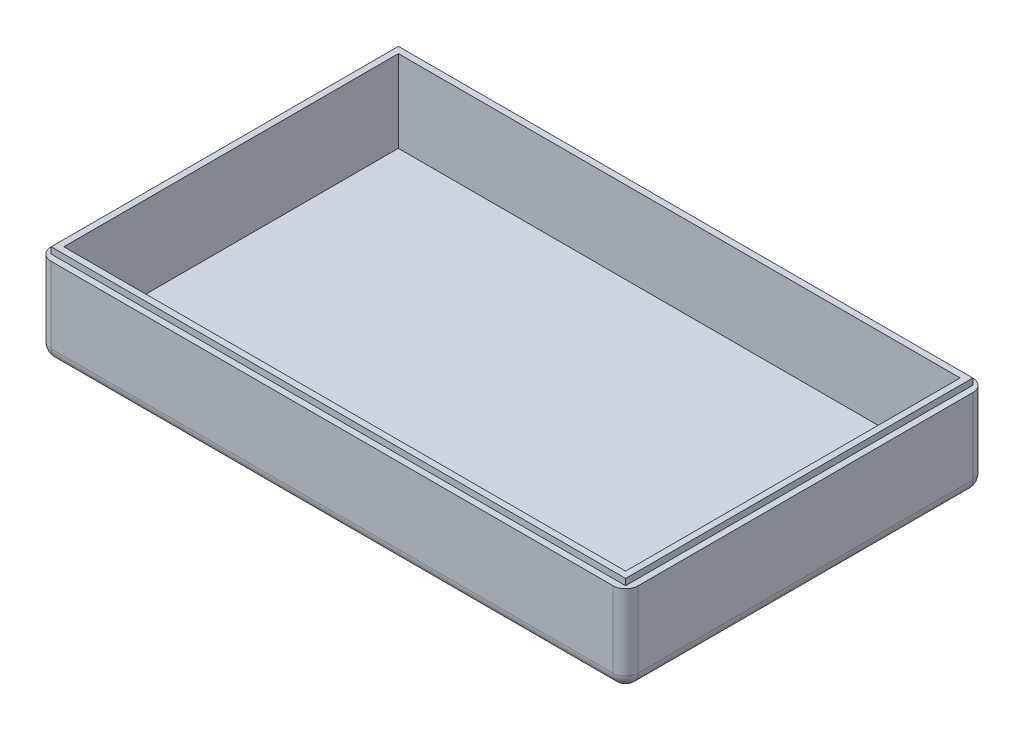
SolidWorks part; units mm, degrees
ref_plane "Front Plane" through (0, 0, 0) normal (0, 0, 1) x (1, 0, 0)
ref_plane "Top Plane" through (0, 0, 0) normal (0, 1, 0) x (1, 0, 0)
ref_plane "Right Plane" through (0, 0, 0) normal (1, 0, 0) x (0, 0, -1)
sketch "Sketch1" plane through (0, 0, 0) normal (0, 1, 0) x (1, 0, 0)
  line L1 (-46.5, -28.5) -> (46.5, -28.5)
  line L2 (-46.5, -28.5) -> (-46.5, 28.5)
  line L3 (-46.5, 28.5) -> (46.5, 28.5)
  line L4 (46.5, -28.5) -> (46.5, 28.5)
  line L5 (-46.5, -28.5) -> (46.5, 28.5) construction
  line L6 (-46.5, 28.5) -> (46.5, -28.5) construction
  point P0 (0, 0)
  dimension "D1" = 93
  dimension "D2" = 57
extrude "Boss-Extrude1" add sketch "Sketch1" along normal blind 14
shell "Shell1" thickness 2
sketch "Sketch2" plane through (0, 14, 0) normal (0, 1, 0) x (1, 0, 0)
  line L0 (-45.5, 27.5) -> (-45.5, -27.5)
  line L1 (-44.5, 26.5) -> (44.5, 26.5)
  line L2 (-44.5, 26.5) -> (-44.5, -26.5)
  line L3 (-44.5, -26.5) -> (44.5, -26.5)
  line L4 (44.5, 26.5) -> (44.5, -26.5)
  line L5 (-45.5, -27.5) -> (45.5, -27.5)
  line L6 (45.5, 27.5) -> (45.5, -27.5)
  line L7 (-45.5, 27.5) -> (45.5, 27.5)
  dimension "D1" = 1
extrude "Boss-Extrude2" add sketch "Sketch2" along normal blind 1
fillet "Fillet2" radius 2 8 edges at (46.5, 7, 28.5) (46.5, 7, -28.5) (46.5, 0, 0) (0, 0, 28.5) (0, 0, -28.5) (-46.5, 7, -28.5) (-46.5, 0, 0) (-46.5, 7, 28.5)
